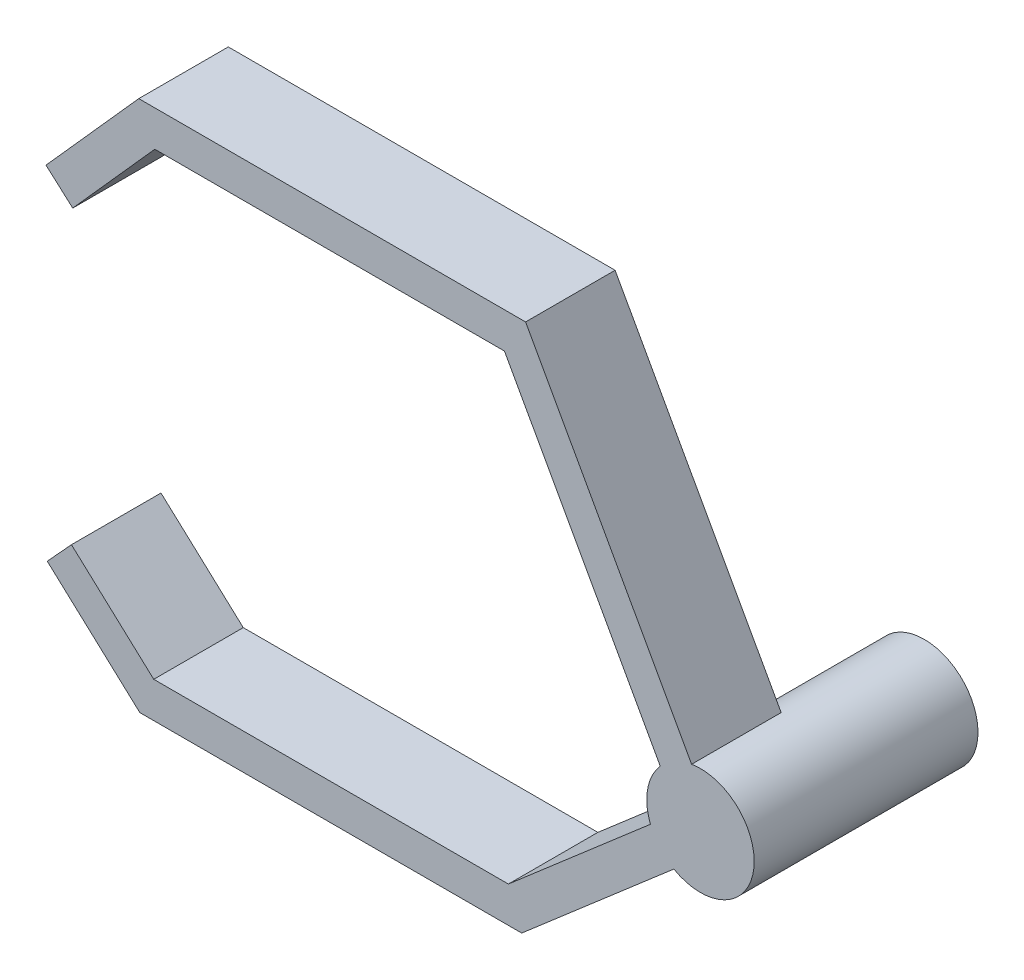
SolidWorks part; units mm, degrees
ref_plane "Front Plane" through (0, 0, 0) normal (0, 0, 1) x (1, 0, 0)
ref_plane "Top Plane" through (0, 0, 0) normal (0, 1, 0) x (1, 0, 0)
ref_plane "Right Plane" through (0, 0, 0) normal (1, 0, 0) x (0, 0, -1)
sketch "Sketch1" plane through (0, 0, 0) normal (0, 0, 1) x (1, 0, 0)
  line L0 (0, 0) -> (-20.715, 37.435) construction
  line L1 (-20.715, 37.435) -> (-61.8491, 37.435) construction
  line L2 (-61.8491, 37.435) -> (-71.6147, 26.4856) construction
  line L3 (0, 0) -> (-20.715, -17.9037) construction
  line L4 (-20.715, -17.9037) -> (-61.8491, -17.9037) construction
  line L5 (-61.8491, -17.9037) -> (-71.6147, -8.9518) construction
  line L6 (-62.627, -19.9037) -> (-72.9662, -10.4261)
  line L7 (-19.9705, -19.9037) -> (-62.627, -19.9037)
  line L8 (2.5358, -0.4518) -> (-19.9705, -19.9037)
  line L9 (2.5358, -0.4518) -> (-19.5359, 39.435)
  line L10 (-19.5359, 39.435) -> (-62.7452, 39.435)
  line L11 (-62.7452, 39.435) -> (-73.1073, 27.8168)
  line L12 (-61.0711, -15.9037) -> (-70.2633, -7.4775)
  line L13 (-21.4595, -15.9037) -> (-61.0711, -15.9037)
  line L14 (-2.5358, 0.4518) -> (-21.4595, -15.9037)
  line L15 (-2.5358, 0.4518) -> (-21.8941, 35.435)
  line L16 (-21.8941, 35.435) -> (-60.953, 35.435)
  line L17 (-60.953, 35.435) -> (-70.1221, 25.1544)
  line L18 (-73.1073, 27.8168) -> (-70.1221, 25.1544)
  line L19 (-70.2633, -7.4775) -> (-72.9662, -10.4261)
  circle A0 centre (0, 0) radius 6
  dimension "D1" = 12
  dimension "D2" = 2
  dimension "D3" = 2
extrude "Boss-Extrude1" add sketch "Sketch1" along normal blind 10 contours A0 L9 L10 L11 L18 L17 L16 L15 | L8 A0 L9 | L9 A0 L15 L14 L8 | A0 L14 L13 L12 L19 L6 L7 L8
sketch "Sketch2" plane through (0, 0, 10) normal (0, 0, 1) x (1, 0, 0)
  circle A0 centre (0, 0) radius 6
extrude "Boss-Extrude2" add sketch "Sketch2" against normal blind 25
